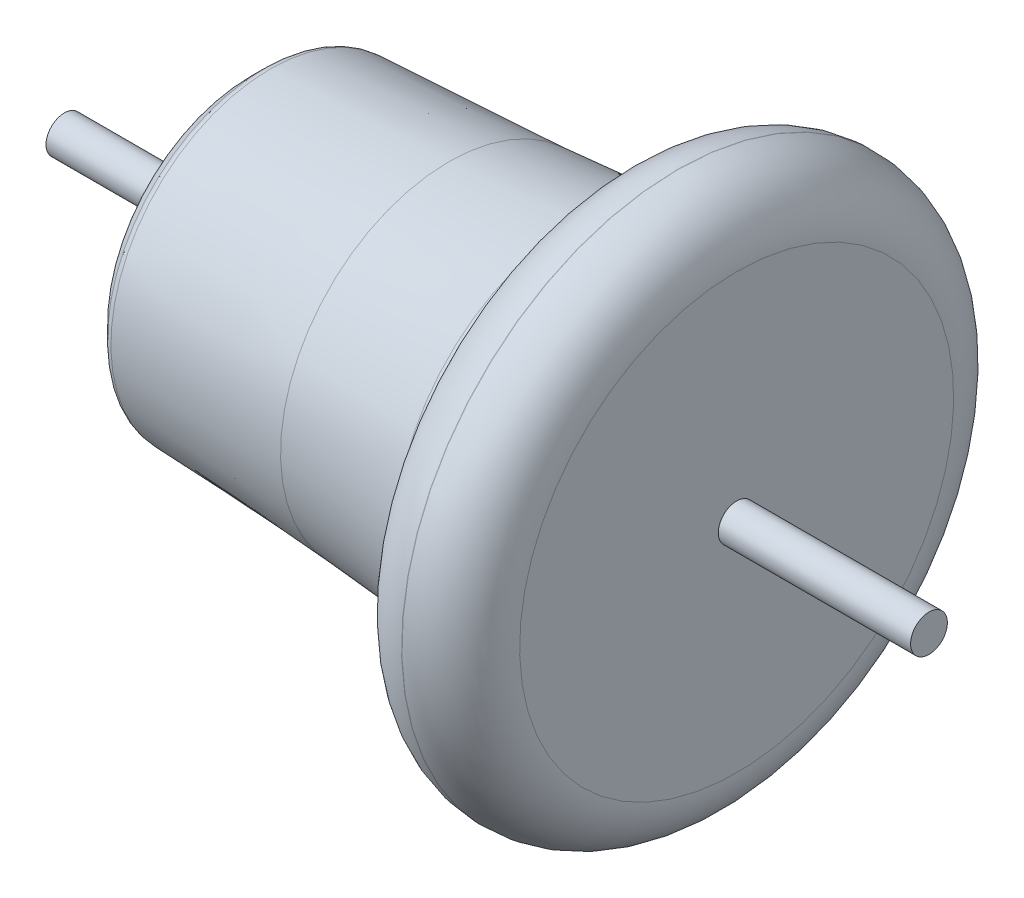
SolidWorks part; units mm, degrees
ref_plane "Front Plane" through (0, 0, 0) normal (0, 0, 1) x (1, 0, 0)
ref_plane "Top Plane" through (0, 0, 0) normal (0, 1, 0) x (1, 0, 0)
ref_plane "Right Plane" through (0, 0, 0) normal (1, 0, 0) x (0, 0, -1)
sketch "Sketch2" plane through (0, 0, 0) normal (0, 0, 1) x (1, 0, 0)
  line L1 (-127.7289, 81.725) -> (0.2711, 81.725) construction
  line L2 (-16, 50) -> (-16, 66) construction
  line L3 (-126.767, 81.6769) -> (-78.2289, 79.25)
  line L4 (0, 78.5) -> (0, 125)
  line L5 (-132.7289, 87.7605) -> (-132.7289, 97.7605)
  line L6 (-132.7289, 87.7605) -> (-132.7289, 97.7605)
  line L9 (-131.9967, 85.9928) -> (-128.41, 82.406)
  line L10 (0, 78.5) -> (0, 66)
  line L11 (-16, 50) -> (-16.0989, 50)
  line L13 (-16, 66) -> (-16.0989, 66)
  line L14 (-63.2289, 78.5) -> (0, 78.5) construction
  line L15 (-16.0989, 66) -> (-16.0989, 50) construction
  line L16 (-32.4125, 63) -> (2.5331, 63) construction
  line L17 (-31.8152, 63) -> (-31.8152, 77.3563) construction
  line L18 (-16.0989, 50) -> (-16, 50)
  line L19 (-132.7289, 92.7605) -> (-118.3038, 92.7605) construction
  line L20 (-32.0568, 63.6638) -> (-32.7542, 65.5799)
  line L21 (-63.2289, 77.2076) -> (-48.7289, 77.2076) construction
  line L22 (-48.7289, 77.2076) -> (-48.7289, 76.3083) construction
  line L23 (-48.7289, 76.3083) -> (-48.7289, 56.553) construction
  line L24 (-128.41, 82.406) -> (-128.41, 125) construction
  line L30 (-132.7289, 97.7605) -> (-132.7289, 125)
  line L31 (-133, 150) -> (-132.7289, 150) construction
  line L39 (-132.7289, 150) -> (-133, 150)
  line L42 (-16, 50) -> (-16, 125)
  line L43 (0, 125) -> (-132.7289, 125)
  arc A0 (-16, 50) -> (0, 66) centre (-16, 66) ccw
  arc A1 (-31.7019, 62.4576) -> (-16.0989, 50) centre (-16.0989, 66) ccw
  arc A4 (-32.7542, 65.5799) -> (-39.1693, 73.823) centre (-48.7289, 59.7655) ccw
  arc A5 (-43.123, 75.4135) -> (-78.2289, 79.25) centre (-93.2102, -220.3757) ccw
  arc A7 (-31.7019, 62.4576) -> (-32.0568, 63.6638) centre (-41.4537, 60.2436) ccw
  arc A8 (-39.1693, 73.823) -> (-43.123, 75.4135) centre (-44.7926, 65.5539) ccw
  arc A9 (-131.9967, 85.9928) -> (-132.7289, 87.7605) centre (-130.2289, 87.7605) cw
  arc A10 (-126.767, 81.6769) -> (-128.41, 82.406) centre (-126.6422, 84.1738) cw
  dimension "D6" = 2.862
  dimension "D3" = 13
  dimension "D2" = 32
  dimension "D4" = 48.5381
  dimension "D5" = 10
  dimension "D8" = 35.1059
  dimension "D9" = 34
  dimension "D10" = 10
  dimension "D11" = 2.5
  dimension "D12" = 2.5
  dimension "D13" = 300
  dimension "D14" = 16.0989
  dimension "D15" = 15.6029
  dimension "D17" = 132.7289
  dimension "D7" = 10
  dimension "D16" = 11.4212
revolve "Revolve1" add sketch "Sketch2" angle 360 about L43
sketch "Sketch3" plane through (-132.7289, 0, 0) normal (-1, 0, 0) x (0, 0, 1)
  circle A0 centre (0, 125) radius 5
  dimension "D1" = 10
extrude "Boss-Extrude1" add sketch "Sketch3" along normal blind 50 and the other way blind 185
